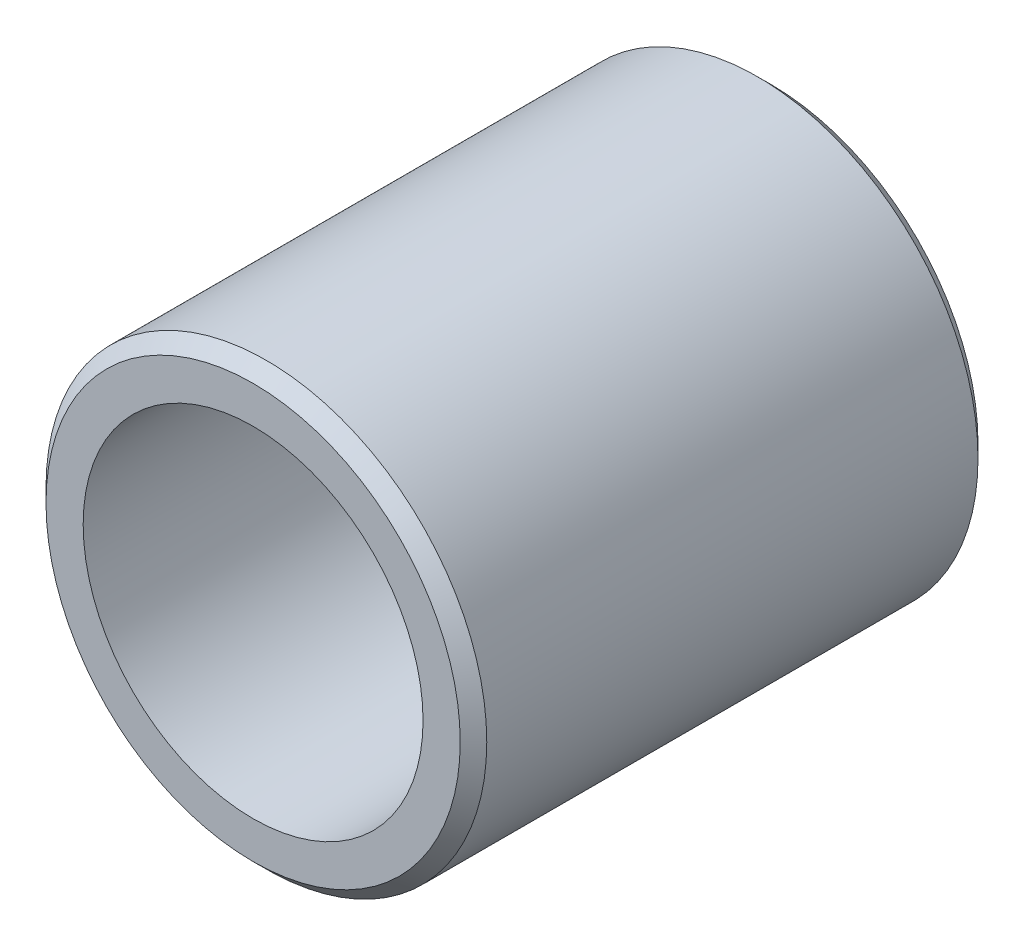
SolidWorks part; units mm, degrees
ref_plane "Plan1" through (0, 0, 0) normal (0, 0, 1) x (1, 0, 0)
ref_plane "Plan2" through (0, 0, 0) normal (0, 1, 0) x (1, 0, 0)
ref_plane "Plan3" through (0, 0, 0) normal (1, 0, 0) x (0, 0, -1)
sketch "Esquisse1" plane through (0, 0, 0) normal (0, 0, 1) x (1, 0, 0)
  circle A0 centre (0, 0) radius 6.4
  circle A1 centre (0, 0) radius 8.3
  dimension "D1" = 16.6
  dimension "D2" = 12.8
extrude "Base-Extrusion" add sketch "Esquisse1" along normal blind 19.5
fillet "Congé1" radius 0.5
chamfer "Chanfrein1" distance 0.5 angle 45
